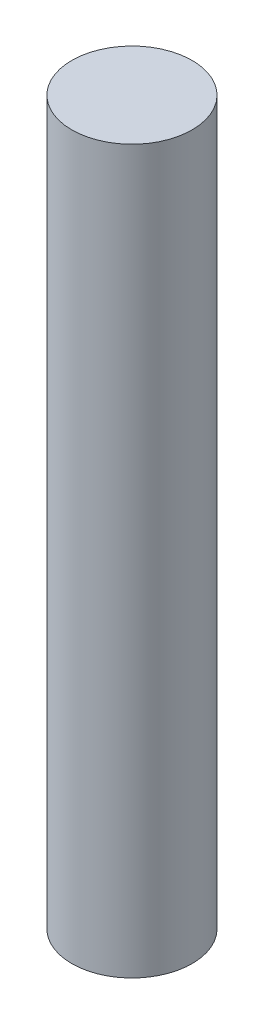
SolidWorks part; units mm, degrees
ref_plane "Front Plane" through (0, 0, 0) normal (0, 0, 1) x (1, 0, 0)
ref_plane "Top Plane" through (0, 0, 0) normal (0, 1, 0) x (1, 0, 0)
ref_plane "Right Plane" through (0, 0, 0) normal (1, 0, 0) x (0, 0, -1)
sketch "Sketch1" plane through (0, 0, 0) normal (0, 1, 0) x (1, 0, 0)
  circle A0 centre (0, 0) radius 3.175
  dimension "D1" = 6.35
extrude "Boss-Extrude1" add sketch "Sketch1" along normal blind 38.1
